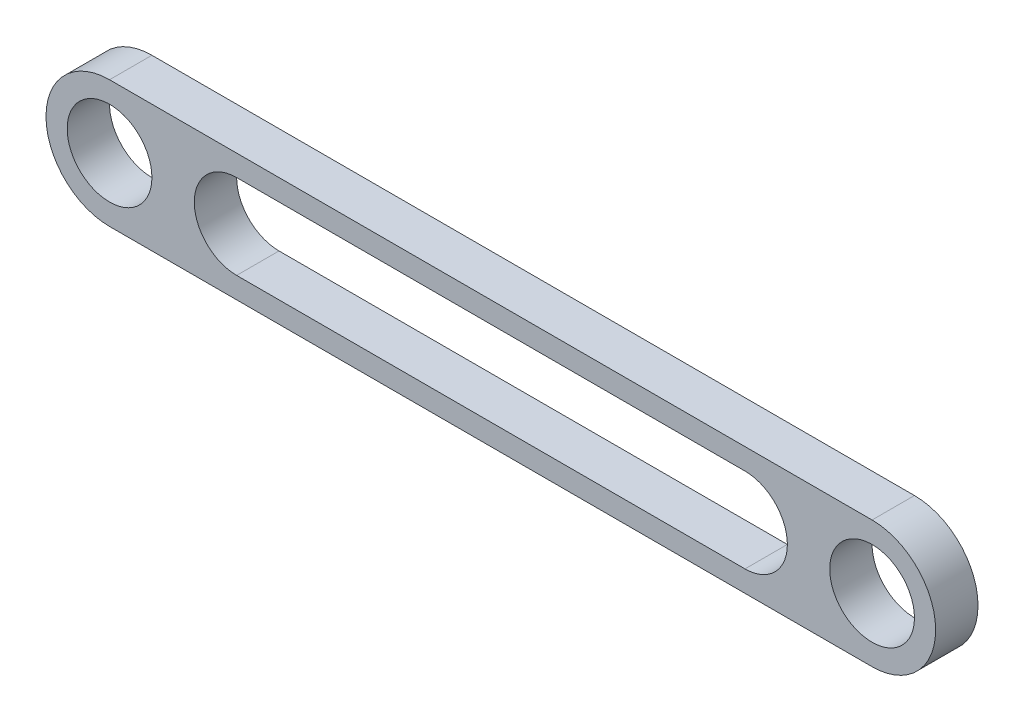
SolidWorks part; units mm, degrees
ref_plane "Front Plane" through (0, 0, 0) normal (0, 0, 1) x (1, 0, 0)
ref_plane "Top Plane" through (0, 0, 0) normal (0, 1, 0) x (1, 0, 0)
ref_plane "Right Plane" through (0, 0, 0) normal (1, 0, 0) x (0, 0, -1)
sketch "Sketch2" plane through (0, 0, 0) normal (0, 0, 1) x (1, 0, 0)
  line L0 (0, 0) -> (180, 0) construction
  line L1 (0, 15) -> (180, 15)
  line L2 (0, -15) -> (180, -15)
  line L3 (30, 10) -> (150, 10)
  line L4 (150, -10) -> (30, -10)
  circle A0 centre (0, 0) radius 10
  circle A1 centre (180, 0) radius 10
  arc A2 (0, 15) -> (0, -15) centre (0, 0) ccw
  arc A3 (180, -15) -> (180, 15) centre (180, 0) ccw
  arc A4 (30, 10) -> (30, -10) centre (30, 0) ccw
  arc A5 (150, -10) -> (150, 10) centre (150, 0) ccw
  dimension "D1" = 20
  dimension "D2" = 20
  dimension "D4" = 30
  dimension "D5" = 30
  dimension "D6" = 20
  dimension "D7" = 20
  dimension "D3" = 180
  dimension "D8" = 30
  dimension "D9" = 30
extrude "Boss-Extrude1" add sketch "Sketch2" along normal blind 10
